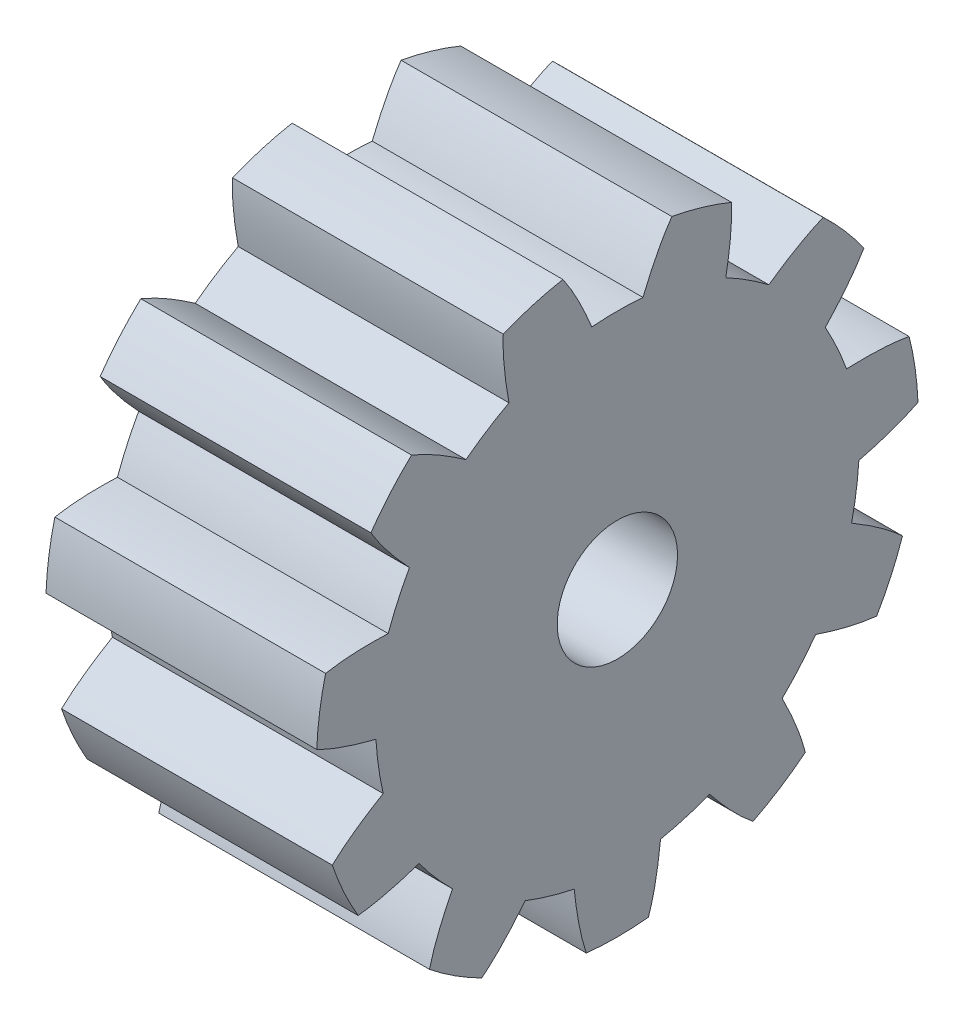
SolidWorks part; units mm, degrees
ref_plane "Front Plane" through (0, 0, 0) normal (0, 0, 1) x (1, 0, 0)
ref_plane "Top Plane" through (0, 0, 0) normal (0, 1, 0) x (1, 0, 0)
ref_plane "Right Plane" through (0, 0, 0) normal (1, 0, 0) x (0, 0, -1)
sketch "Sketch2" plane through (0, 0, 0) normal (1, 0, 0) x (0, 0, -1)
  circle A0 centre (0, 0) radius 10
  arc A1 (2.2589, 9.7415) -> (-2.2589, 9.7415) centre (0, 0) ccw
  circle A2 centre (0, 0) radius 1
  dimension "D1" = 2
extrude "Boss-Extrude2" add sketch "Sketch2" along normal blind 9 contours A0 A2
sketch "Sketch6" plane through (0, 0, 0) normal (1, 0, 0) x (0, 0, -1)
  arc A0 (1.85, 9.8897) -> (-1.85, 9.8897) centre (0, -2.6089) ccw
  arc A2 (0.85, 7.987) -> (-0.85, 7.987) centre (0, -2.6089) ccw
  spline S0 degree 3 poles (0.85, 7.987) (1.1333, 8.6722) (1.4465, 9.3265) (1.85, 9.8897) knots 0.309355 0.309355 0.309355 0.309355 0.515064 0.515064 0.515064 0.515064
  spline S3 degree 3 poles (-0.85, 7.987) (-1.1333, 8.6722) (-1.4465, 9.3265) (-1.85, 9.8897) knots 0.309355 0.309355 0.309355 0.309355 0.515064 0.515064 0.515064 0.515064
  dimension "D1" = 1.7
  dimension "D2" = 3.7
extrude "Cut-Extrude4" cut sketch "Sketch6" against normal blind 10 and the other way through all
pattern_circular "CirPattern2" count 11 over 360 about axis through (9, 0, 0) along (-1, 0, 0) of "Cut-Extrude4"
sketch "Sketch7" plane through (9, 0, 0) normal (1, 0, 0) x (0, 0, -1)
  circle A0 centre (0, 0) radius 1 construction
  circle A1 centre (0, 0) radius 1
  circle A2 centre (0, 0) radius 2
extrude "Cut-Extrude5" cut sketch "Sketch7" against normal blind 7.5
sketch "Sketch9" plane through (0, 0, 0) normal (-1, 0, 0) x (0, 0, 1)
  arc A0 (-1.0331, -9.9465) -> (1.0331, -9.9465) centre (0, 0) ccw construction
  arc A1 (-1.0331, -9.9465) -> (1.0331, -9.9465) centre (0, 0) ccw
  circle A2 centre (0, 0) radius 10 construction
  spline S0 degree 3 poles (1782.5374, 894.2732) (-1779.7775, -992.6036) (1777.8076, 977.8435) (-1788.9095, -904.1885) knots -5.296691 -5.296691 -5.296691 -5.296691 6.521325 6.521325 6.521325 6.521325 only from (-1.0331, -9.9465) to (-1.4346, -7.9029) construction
  spline S1 degree 3 poles (1788.9103, -904.1889) (-1777.8055, 977.8425) (1779.7726, -992.6009) (-1782.5298, 894.2692) knots -5.696907 -5.696907 -5.696907 -5.696907 6.121101 6.121101 6.121101 6.121101 only from (1.4346, -7.9029) to (1.0331, -9.9465) construction
  spline S2 degree 3 poles (-1.0331, -9.9465) (-1.2472, -9.3098) (-1.3584, -8.6163) (-1.4346, -7.9029) knots 0.309355 0.309355 0.309355 0.309355 0.508394 0.508394 0.508394 0.508394
  spline S3 degree 3 poles (1.4346, -7.9029) (1.3584, -8.6163) (1.2472, -9.3098) (1.0331, -9.9465) knots 0.316025 0.316025 0.316025 0.316025 0.515064 0.515064 0.515064 0.515064
